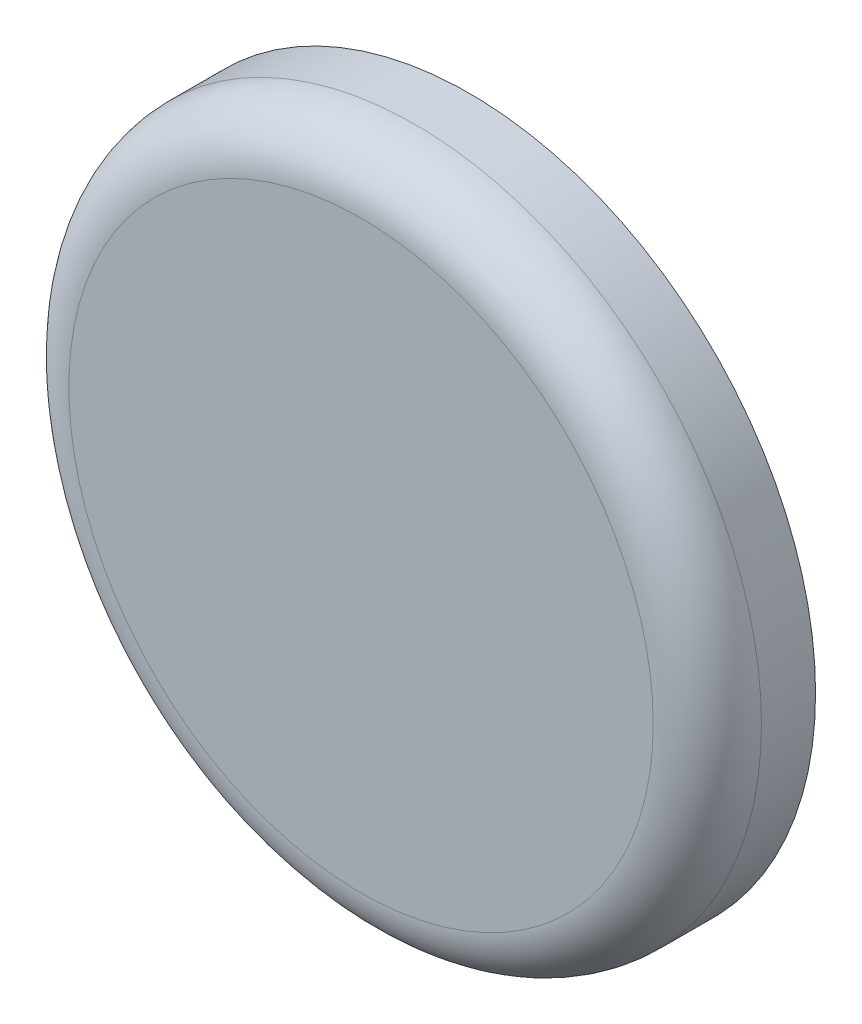
SolidWorks part; units mm, degrees
ref_plane "Plano frontal" through (0, 0, 0) normal (0, 0, 1) x (1, 0, 0)
ref_plane "Plano superior" through (0, 0, 0) normal (0, 1, 0) x (1, 0, 0)
ref_plane "Plano direito" through (0, 0, 0) normal (1, 0, 0) x (0, 0, -1)
sketch "Esboço1" plane through (0, 0, 0) normal (0, 0, 1) x (1, 0, 0)
  circle A0 centre (0, 0) radius 32
extrude "Ressalto-extrusão1" add sketch "Esboço1" along normal blind 10
fillet "Filete1" radius 5 1 edges at (32, 0, 10)
sketch "Esboço2" plane through (0, 0, 0) normal (0, 0, -1) x (-1, 0, 0)
  circle A0 centre (0, 0) radius 27
extrude "Corte-extrusão1" cut sketch "Esboço2" against normal blind 5
